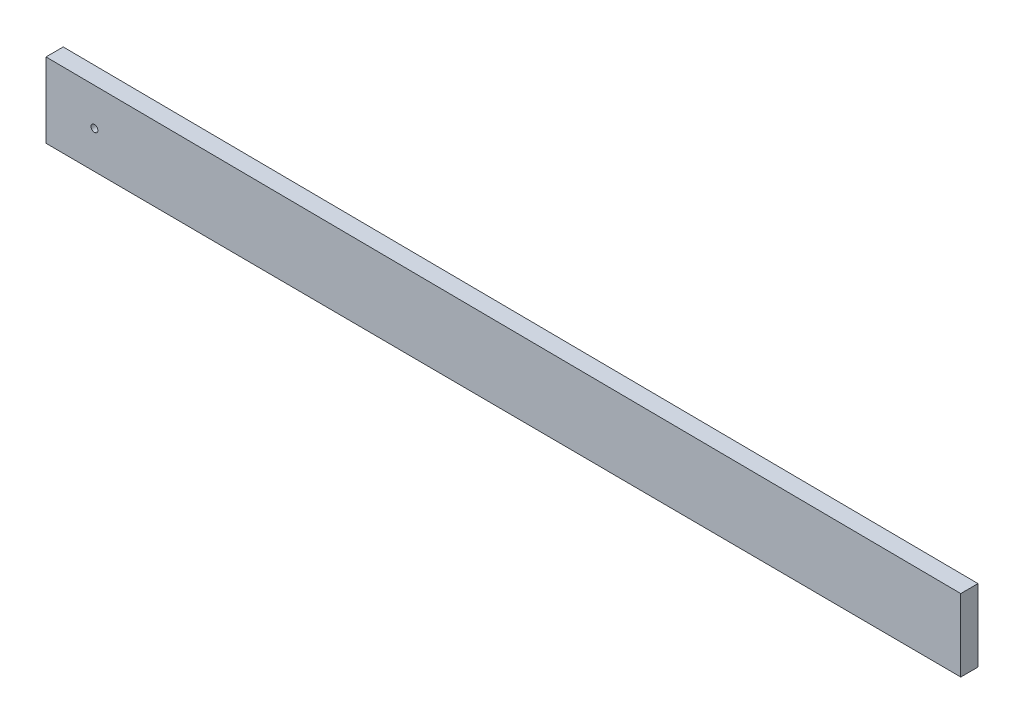
SolidWorks part; units mm, degrees
ref_plane "Front Plane" through (0, 0, 0) normal (0, 0, 1) x (1, 0, 0)
ref_plane "Top Plane" through (0, 0, 0) normal (0, 1, 0) x (1, 0, 0)
ref_plane "Right Plane" through (0, 0, 0) normal (1, 0, 0) x (0, 0, -1)
sketch "Sketch1" plane through (0, 0, 0) normal (0, 0, 1) x (1, 0, 0)
  line L2 (1.5875, 128.193) -> (1.5875, 141.9551)
  line L3 (169.8625, 127.2918) -> (169.8625, 140.5971)
  line L4 (169.8625, 127.2918) -> (1.5875, 128.193)
  line L5 (1.5875, 141.9551) -> (169.8625, 140.5971)
  circle A0 centre (10.4954, 135.0183) radius 0.635
  dimension "D1" = 1.27
extrude "Boss-Extrude1" add sketch "Sketch1" against normal blind 3.175 contours L5 L2 L4 L3
